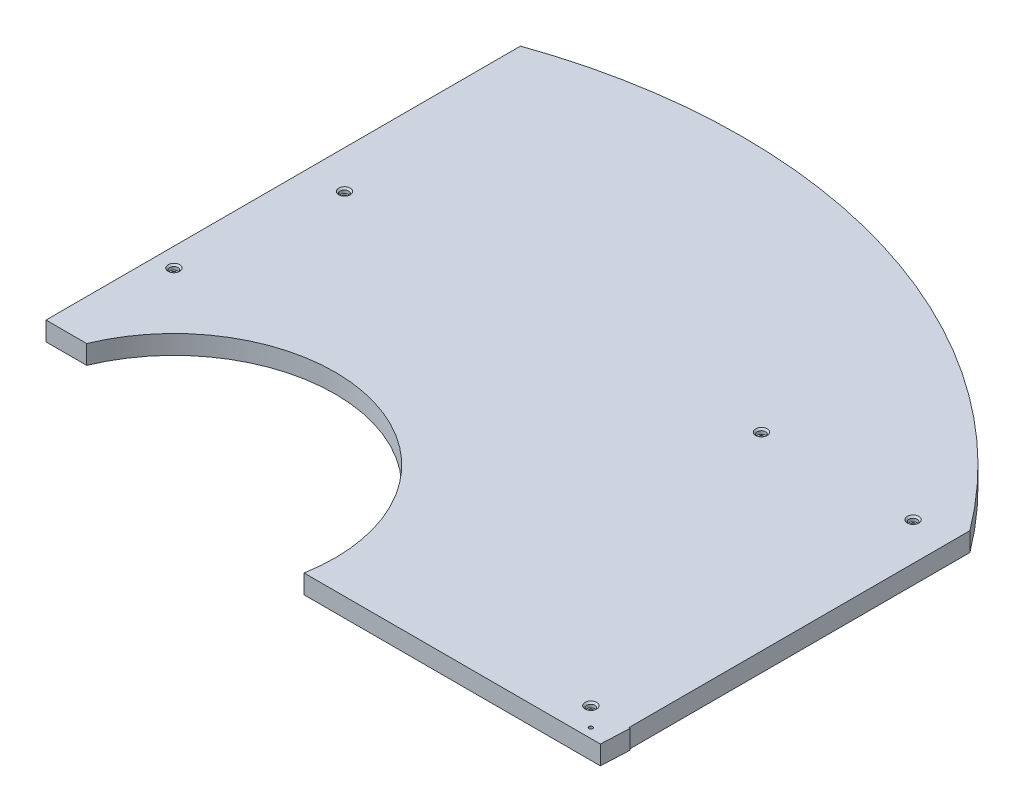
SolidWorks part; units mm, degrees
ref_plane "Front" through (0, 0, 0) normal (0, 0, 1) x (1, 0, 0)
ref_plane "Top" through (0, 0, 0) normal (0, 1, 0) x (1, 0, 0)
ref_plane "Right" through (0, 0, 0) normal (1, 0, 0) x (0, 0, -1)
sketch "Sketch2" plane through (0, 0, 0) normal (0, 1, 0) x (1, 0, 0)
  line L0 (-381.1798, 499.0548) -> (-381.1798, -186.1347) construction
  line L1 (-406.5798, 524.4548) -> (1600.0202, 524.4548)
  line L2 (-406.5798, 524.4548) -> (-406.5798, -237.5452)
  line L3 (-406.5798, -237.5452) -> (1600.0202, -237.5452)
  line L4 (1600.0202, 524.4548) -> (1600.0202, -237.5452)
  line L5 (-381.1798, 499.0548) -> (223.3824, 499.0548) construction
  dimension "D1" = 762
  dimension "D2" = 2006.6
  dimension "D3" = 25.4
  dimension "D4" = 25.4
extrude "Boss-Extrude1" add sketch "Sketch2" along normal blind 25.4
sketch "Cut Lines" plane through (0, 25.4, 0) normal (0, 1, 0) x (1, 0, 0)
  line L0 (761.8202, 219.6548) -> (761.8202, -554.7005) construction
  line L1 (-406.5798, -237.5452) -> (1600.0202, -237.5452) construction
  line L2 (1600.0202, -237.5452) -> (1600.0202, 524.4548) construction
  line L3 (-406.5798, -237.5452) -> (1600.0202, -237.5452)
  line L4 (-406.5798, -237.5452) -> (-406.5798, 219.6548)
  line L5 (-406.5798, 219.6548) -> (1600.0202, 219.6548)
  line L6 (1600.0202, -237.5452) -> (1600.0202, 219.6548)
  line L7 (1600.0202, 524.4548) -> (-406.5798, 524.4548) construction
  line L8 (-406.5798, -237.5452) -> (-127.1798, -237.5452)
  line L9 (-406.5798, -237.5452) -> (-406.5798, 524.4548)
  line L10 (-406.5798, 524.4548) -> (-127.1798, 524.4548)
  line L12 (-101.7798, 604.8973) -> (-101.7798, -376.747) construction
  line L13 (-406.5798, -237.5452) -> (-25.5798, -237.5452)
  line L14 (-406.5798, -237.5452) -> (-406.5798, -154.9952)
  line L15 (-406.5798, -154.9952) -> (-25.5798, -154.9952)
  line L16 (-25.5798, -237.5452) -> (-25.5798, -154.9952)
  circle A0 centre (152.2202, -237.5452) radius 215.9
  circle A1 centre (152.2202, -237.5452) radius 762
  dimension "D1" = 431.8
  dimension "D4" = 558.8
  dimension "D2" = 254
  dimension "D3" = 457.2
  dimension "D5" = 82.55
  dimension "D6" = 381
sketch "Sketch63" plane through (0, 25.4, 0) normal (0, 1, 0) x (1, 0, 0)
  line L0 (-406.5798, -237.5452) -> (1600.0202, -237.5452) construction
  line L1 (368.1202, -237.5452) -> (763.5508, -237.5452)
  line L2 (763.5508, -237.5452) -> (761.8202, -275.6452)
  line L3 (761.8202, 219.6548) -> (761.8202, -554.7005) construction
  line L4 (761.8202, -275.6452) -> (364.7319, -275.6452)
  arc A0 (364.7319, -275.6452) -> (368.1202, -237.5452) centre (152.2202, -237.5452) ccw
  circle A1 centre (152.2202, -237.5452) radius 215.9 construction
  dimension "D1" = 38.1
extrude "Boss-Extrude4" add sketch "Sketch63" against normal blind 25.4
sketch "Sketch64" plane through (0, 25.4, 0) normal (0, 1, 0) x (1, 0, 0)
  line L0 (736.4202, 256.8794) -> (736.4202, -353.4641) construction
  line L1 (823.2583, -262.9452) -> (80.2315, -262.9452) construction
  line L2 (761.8202, 219.6548) -> (761.8202, -554.7005) construction
  line L3 (364.7319, -275.6452) -> (761.8202, -275.6452) construction
  dimension "D1" = 25.4
  dimension "D2" = 12.7
hole_wizard "1/4-20 Tapped Hole1" positions "Sketch66" profile "Sketch65" tap size "1/4-20" standard "ANSI Inch" end condition through all
sketch "Sketch66" plane through (0, 25.4, 0) normal (0, 1, 0) x (1, 0, 0)
  line L0 (736.4202, 256.8794) -> (736.4202, -353.4641) construction
  line L1 (823.2583, -262.9452) -> (80.2315, -262.9452) construction
  point P0 (736.4202, -262.9452)
sketch "Sketch65" plane through (736.4202, 25.4, 262.9452) normal (1, 0, 0) x (0, 0, 1)
  line L0 (0, 0) -> (0, 25.4001)
  line L1 (0, 25.4001) -> (2.5527, 25.4001)
  line L2 (2.5527, 25.4001) -> (2.5527, 0)
  line L5 (2.5527, 0) -> (0, 0)
  line L11 (0, -6.35) -> (0, 107.95) construction
  dimension "Thru Tap Drill Dia." = 5.1054
  dimension "Thru Tap Drill Depth" = 25.4001
cosmetic thread "Hole Thread1" parameters "D2"=6.35
pattern_linear "LPattern1" [suppressed] count 31 spacing 25.4 along (0, 0, 1) count 40 spacing 25.4 along (-1, 0, 0)
sketch "Sketch5" plane through (0, 25.4, 0) normal (0, 1, 0) x (1, 0, 0)
  line L0 (-406.5798, -237.5452) -> (368.1202, -237.5452) construction
  circle A0 centre (152.2202, -237.5452) radius 215.9
  circle A1 centre (152.2202, -237.5452) radius 215.9 construction
  dimension "D1" = 431.8
  dimension "D2" = 0
extrude "Cut-Extrude2" cut sketch "Sketch5" against normal through all
sketch "Sketch6" plane through (0, 25.4, 0) normal (0, 1, 0) x (1, 0, 0)
  line L1 (-406.5798, -237.5452) -> (-25.5798, -237.5452)
  line L2 (-406.5798, -237.5452) -> (-406.5798, -154.9952)
  line L3 (-406.5798, -154.9952) -> (-25.5798, -154.9952)
  line L4 (-25.5798, -237.5452) -> (-25.5798, -154.9952)
  dimension "D1" = 82.55
  dimension "D2" = 381
sketch "Assembly Ref" plane through (0, 25.4, 0) normal (0, 1, 0) x (1, 0, 0)
  line L0 (152.2202, -237.5452) -> (152.2202, 1138.4286) construction
  line L1 (76.0202, -313.7452) -> (228.4202, -313.7452)
  line L2 (76.0202, -313.7452) -> (76.0202, -161.3452)
  line L3 (76.0202, -161.3452) -> (228.4202, -161.3452)
  line L4 (228.4202, -313.7452) -> (228.4202, -161.3452)
  line L5 (76.0202, -313.7452) -> (228.4202, -161.3452) construction
  line L6 (76.0202, -161.3452) -> (228.4202, -313.7452) construction
  line L7 (-736.7798, -85.1452) -> (406.2202, -85.1452)
  line L8 (-736.7798, -85.1452) -> (-736.7798, -389.9452)
  line L9 (-736.7798, -389.9452) -> (406.2202, -389.9452)
  line L10 (406.2202, -85.1452) -> (406.2202, -389.9452)
  line L11 (-986.8428, 346.6548) -> (2392.7723, 346.6548)
  line L12 (-986.8428, 346.6548) -> (-986.8428, -847.1452)
  line L13 (-986.8428, -847.1452) -> (2392.7723, -847.1452)
  line L14 (2392.7723, 346.6548) -> (2392.7723, -847.1452)
  line L15 (533.2202, 219.6548) -> (-76.3798, 219.6548)
  line L16 (533.2202, 219.6548) -> (533.2202, -694.7452)
  line L17 (533.2202, -694.7452) -> (-76.3798, -694.7452)
  line L18 (-76.3798, 219.6548) -> (-76.3798, -694.7452)
  line L19 (152.2202, -237.5452) -> (-471.8049, 386.4799) construction
  line L20 (152.2202, -237.5452) -> (698.8058, 309.0403) construction
  point P0 (152.2202, -237.5452)
  dimension "D1" = 152.4
  dimension "D2" = 152.4
  dimension "D3" = 1143
  dimension "D4" = 304.8
  dimension "D5" = 152.4
  dimension "D6" = 254
  dimension "D7" = 1193.8
  dimension "D8" = 584.2
  dimension "D9" = 228.6
  dimension "D10" = 457.2
  dimension "D11" = 914.4
  dimension "D12" = 609.6
sketch "Sketch10" plane through (0, 25.4, 0) normal (0, 1, 0) x (1, 0, 0)
  line L1 (-406.5798, 524.4548) -> (-101.7798, 524.4548)
  line L2 (-406.5798, 524.4548) -> (-406.5798, -237.5452)
  line L3 (-406.5798, -237.5452) -> (-101.7798, -237.5452)
  line L4 (-101.7798, 524.4548) -> (-101.7798, -237.5452)
  dimension "D1" = 254
  dimension "D2" = 762
extrude "Cut-Extrude5" cut sketch "Sketch10" against normal through all
sketch "Sketch31" plane through (0, 25.4, 0) normal (0, 1, 0) x (1, 0, 0)
  line L1 (-406.5798, -237.5452) -> (-25.5798, -237.5452)
  line L2 (-406.5798, -237.5452) -> (-406.5798, -154.9952)
  line L3 (-406.5798, -154.9952) -> (-25.5798, -154.9952)
  line L4 (-25.5798, -237.5452) -> (-25.5798, -154.9952)
extrude "Cut-Extrude8" cut sketch "Sketch31" against normal through all
sketch "Sketch32" plane through (0, 25.4, 0) normal (0, 1, 0) x (1, 0, 0)
  line L0 (-101.7798, 604.8973) -> (-101.7798, -376.747) construction
  line L1 (-406.5798, 219.6548) -> (1600.0202, 219.6548) construction
  line L2 (761.8202, 219.6548) -> (761.8202, -237.5452)
  line L3 (-406.5798, -237.5452) -> (1600.0202, -237.5452) construction
  line L4 (761.8202, -237.5452) -> (1600.0202, -237.5452)
  line L5 (1600.0202, -237.5452) -> (1600.0202, 524.4548)
  line L6 (1600.0202, 524.4548) -> (-101.7798, 524.4548)
  line L7 (1600.0202, 524.4548) -> (-101.7798, 524.4548) construction
  line L8 (-101.7798, 524.4548) -> (-101.7798, 480.8753)
  arc A0 (-101.7798, 480.8753) -> (761.8202, 219.6548) centre (152.2202, -237.5452) ccw
  circle A1 centre (152.2202, -237.5452) radius 762 construction
sketch "Sketch39" plane through (0, 25.4, 0) normal (0, 1, 0) x (1, 0, 0)
  line L0 (1600.0202, 524.4548) -> (-101.7798, 524.4548) construction
  line L1 (-101.7798, 604.8973) -> (-101.7798, -376.747) construction
  line L2 (-101.7798, 480.8753) -> (-101.7798, 524.4548)
  line L3 (-101.7798, 524.4548) -> (152.2202, 524.4548)
  arc A0 (152.2202, 524.4548) -> (-101.7798, 480.8753) centre (152.2202, -237.5452) ccw
  circle A1 centre (152.2202, -237.5452) radius 762 construction
extrude "Cut-Extrude9" cut sketch "Sketch39" against normal through all
sketch "Sketch40" plane through (0, 25.4, 0) normal (0, 1, 0) x (1, 0, 0)
  line L0 (152.2202, 524.4548) -> (1600.0202, 524.4548)
  line L1 (1600.0202, 524.4548) -> (1600.0202, 219.6548)
  line L2 (1600.0202, 219.6548) -> (761.8202, 219.6548)
  arc A0 (761.8202, 219.6548) -> (152.2202, 524.4548) centre (152.2202, -237.5452) ccw
extrude "Cut-Extrude10" cut sketch "Sketch40" against normal through all
sketch "Sketch41" plane through (0, 25.4, 0) normal (0, 1, 0) x (1, 0, 0)
  line L0 (761.8202, 219.6548) -> (1600.0202, 219.6548)
  line L1 (1600.0202, 219.6548) -> (1600.0202, -237.5452)
  line L2 (1600.0202, -237.5452) -> (761.8202, -237.5452)
  line L3 (761.8202, -237.5452) -> (761.8202, 219.6548)
extrude "Cut-Extrude11" cut sketch "Sketch41" against normal through all
hole_wizard "CBORE for 1/4 Socket Head Cap Screw1" positions "Sketch68" profile "Sketch67" counterbore size "1/4" standard "ANSI Inch" end condition through all
sketch "Sketch68" plane through (0, 25.4, 0) normal (0, 1, 0) x (1, 0, 0)
  line L0 (-76.3798, 219.6548) -> (-76.3798, -694.7452) construction
  line L2 (-406.5798, 219.6548) -> (1600.0202, 219.6548) construction
  line L3 (533.2202, 219.6548) -> (533.2202, -694.7452) construction
  line L4 (-101.7798, 604.8973) -> (-101.7798, -376.747) construction
  line L5 (-406.5798, -237.5452) -> (1600.0202, -237.5452) construction
  line L6 (364.7319, -275.6452) -> (761.8202, -275.6452) construction
  line L7 (761.8202, 219.6548) -> (761.8202, -554.7005) construction
  point P0 (-76.3798, -8.9452)
  point P2 (-50.9798, 194.2548)
  point P4 (507.8202, 194.2548)
  point P6 (711.0202, -237.5452)
  point P8 (711.0202, 194.2548)
  dimension "D1" = 25.4
  dimension "D2" = 25.4
  dimension "D3" = 25.4
  dimension "D4" = 25.4
  dimension "D5" = 25.4
  dimension "D6" = 228.6
  dimension "D7" = 38.1
  dimension "D8" = 50.8
  dimension "D9" = 50.8
  dimension "D10" = 25.4
sketch "Sketch67" plane through (-76.3798, 25.4, 8.9452) normal (1, 0, 0) x (0, 0, 1)
  line L0 (0, 0) -> (0, 25.4001)
  line L1 (0, 25.4001) -> (3.3782, 25.4001)
  line L3 (3.3782, 25.4001) -> (3.3782, 6.35)
  line L4 (5.5562, 6.35) -> (3.3782, 6.35)
  line L5 (5.5562, 6.35) -> (5.5562, 2.2225)
  line L6 (5.5562, 2.2225) -> (7.7788, 0)
  line L7 (7.7788, 0) -> (0, 0)
  line L8 (-5.5562, 2.2225) -> (-7.7788, 0) construction
  line L11 (0, -6.35) -> (0, 107.95) construction
  dimension "Thru Hole Dia." = 6.7564
  dimension "Thru Hole Depth" = 25.4001
  dimension "C'Bore Dia." = 11.1125
  dimension "C'Bore Depth" = 6.35
  dimension "Near C'Sink Dia." = 15.5575
  dimension "Near C'Sink Angle" = 90
